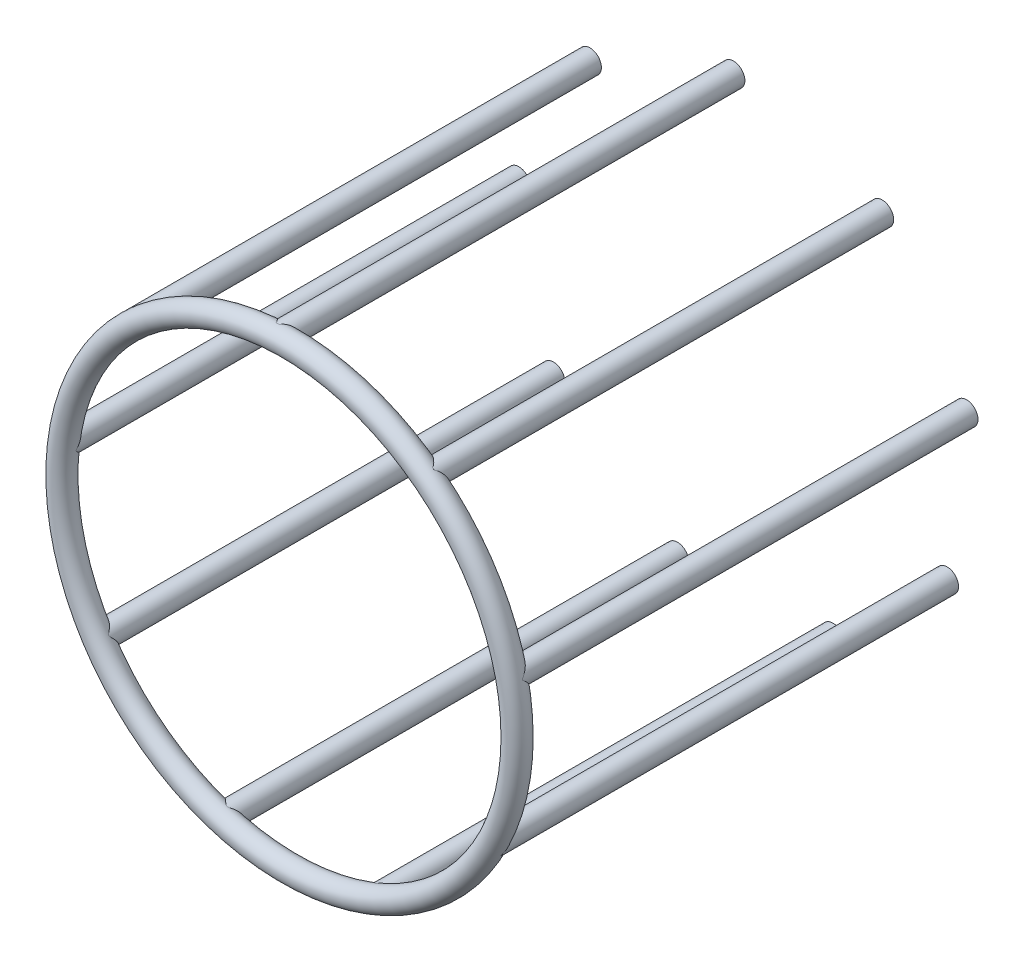
SolidWorks part; units mm, degrees
ref_plane "Ebene Unten" through (0, 0, 0) normal (0, 0, 1) x (1, 0, 0)
ref_plane "Ebene Links" through (0, 0, 0) normal (0, 1, 0) x (1, 0, 0)
ref_plane "Ebene Vorne" through (0, 0, 0) normal (1, 0, 0) x (0, 0, -1)
sketch "Skizze1" plane through (0, 0, 0) normal (0, 0, 1) x (1, 0, 0)
  line L0 (30.2168, 39.8365) -> (48.7538, 11.0936) construction
  line L1 (48.7538, 11.0936) -> (44.4784, -22.8402) construction
  line L2 (44.4784, -22.8402) -> (19.3911, -46.0867) construction
  line L3 (19.3911, -46.0867) -> (-14.7696, -47.7688) construction
  line L4 (-14.7696, -47.7688) -> (-42.0193, -27.0993) construction
  line L5 (-42.0193, -27.0993) -> (-49.6078, 6.2502) construction
  line L6 (-49.6078, 6.2502) -> (-33.9842, 36.6752) construction
  line L7 (-33.9842, 36.6752) -> (-2.459, 49.9395) construction
  line L8 (-2.459, 49.9395) -> (30.2168, 39.8365) construction
  circle A0 centre (0, 0) radius 50 construction
  circle A1 centre (-42.0193, -27.0993) radius 2.5
  circle A2 centre (-14.7696, -47.7688) radius 2.5
  circle A3 centre (19.3911, -46.0867) radius 2.5
  circle A4 centre (44.4784, -22.8402) radius 2.5
  circle A5 centre (48.7538, 11.0936) radius 2.5
  circle A6 centre (30.2168, 39.8365) radius 2.5
  circle A7 centre (-2.459, 49.9395) radius 2.5
  circle A8 centre (-33.9842, 36.6752) radius 2.5
  circle A9 centre (-49.6078, 6.2502) radius 2.5
  dimension "D1" = 5
  dimension "D2" = 100
extrude "Aufsatz-Linear austragen1" add sketch "Skizze1" along normal blind 100
ref_plane "Ebene1" through (0, 0, 100) normal (0, 0, 1) x (1, 0, 0)
sketch "Skizze2" plane through (0, 0, 100) normal (0, 0, 1) x (1, 0, 0)
  circle A0 centre (0, 0) radius 50
  point P0 (30.2168, 39.8365)
sweep "Austragung1" add path "Skizze2" circular profile diameter 5 parameters "D3"=5
